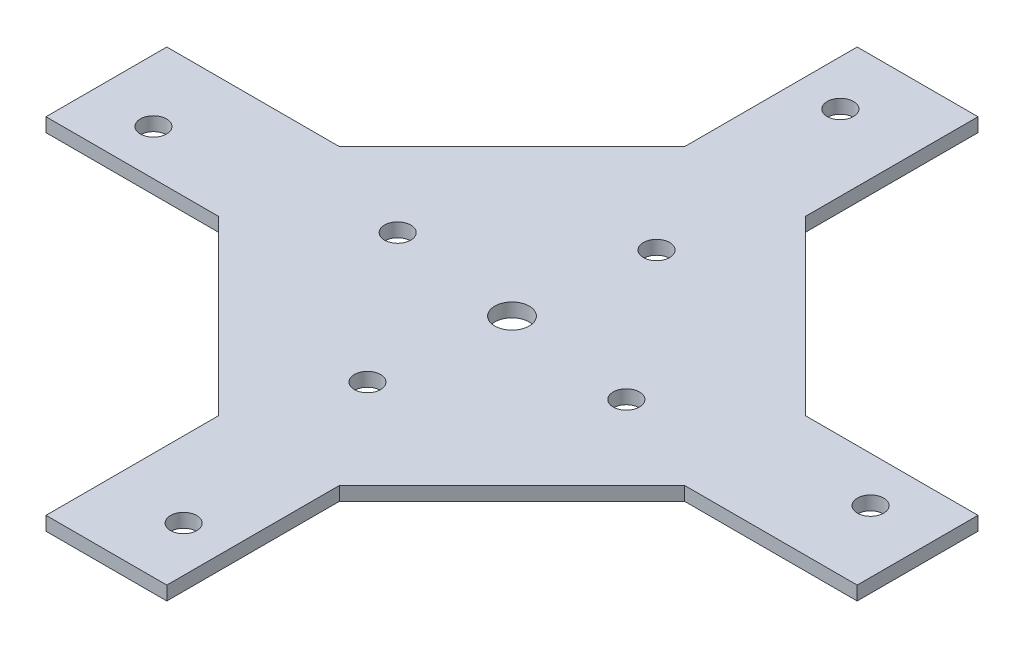
SolidWorks part; units mm, degrees
material "1023 Carbon Steel Sheet (SS)"
ref_plane "Front Plane" through (0, 0, 0) normal (0, 0, 1) x (1, 0, 0)
ref_plane "Top Plane" through (0, 0, 0) normal (0, 1, 0) x (1, 0, 0)
ref_plane "Right Plane" through (0, 0, 0) normal (1, 0, 0) x (0, 0, -1)
sketch "Sketch1" plane through (0, 0, 0) normal (0, 1, 0) x (1, 0, 0)
  line L0 (0, 125.4843) -> (0, -125.4843) construction
  line L2 (173.282, 0) -> (-173.282, 0) construction
  line L3 (-74.6125, -11.1125) -> (-74.6125, 11.1125)
  line L4 (-74.6125, 11.1125) -> (-42.8625, 11.1125)
  line L5 (-74.6125, -11.1125) -> (-42.8625, -11.1125)
  line L6 (-63.1825, -2.7781) -> (-63.1825, 0) construction
  line L7 (-23.8125, 2.7781) -> (-23.8125, 0) construction
  line L8 (-63.1825, -2.7781) -> (0, -2.7781) construction
  line L9 (-23.8125, 2.7781) -> (0, 2.7781) construction
  line L11 (11.1125, 74.6125) -> (11.1125, 42.8625)
  line L12 (-11.1125, 74.6125) -> (11.1125, 74.6125)
  line L13 (-11.1125, 74.6125) -> (-11.1125, 42.8625)
  line L15 (74.6125, -11.1125) -> (42.8625, -11.1125)
  line L16 (74.6125, 11.1125) -> (74.6125, -11.1125)
  line L17 (74.6125, 11.1125) -> (42.8625, 11.1125)
  line L19 (-11.1125, -74.6125) -> (-11.1125, -42.8625)
  line L20 (11.1125, -74.6125) -> (-11.1125, -74.6125)
  line L21 (11.1125, -74.6125) -> (11.1125, -42.8625)
  line L22 (-42.8625, 11.1125) -> (-11.1125, 42.8625) construction
  line L23 (11.1125, 42.8625) -> (42.8625, 11.1125) construction
  line L24 (42.8625, -11.1125) -> (11.1125, -42.8625) construction
  line L25 (-11.1125, -42.8625) -> (-42.8625, -11.1125) construction
  line L26 (-42.8625, 11.1125) -> (-11.1125, 42.8625)
  line L30 (11.1125, 42.8625) -> (42.8625, 11.1125)
  line L31 (42.8625, -11.1125) -> (11.1125, -42.8625)
  line L32 (-42.8625, -11.1125) -> (-11.1125, -42.8625)
  circle A0 centre (-23.8125, 2.7781) radius 2.413
  circle A1 centre (-63.1825, -2.7781) radius 2.413
  circle A8 centre (-2.7781, 63.1825) radius 2.413
  circle A9 centre (2.7781, 23.8125) radius 2.413
  circle A10 centre (63.1825, 2.7781) radius 2.413
  circle A11 centre (23.8125, -2.7781) radius 2.413
  circle A12 centre (2.7781, -63.1825) radius 2.413
  circle A13 centre (-2.7781, -23.8125) radius 2.413
  point P37 (0, 0)
  point P44 (0, 0)
  dimension "D1" = 23.8125
  dimension "D2" = 63.1825
  dimension "D5" = 4.826
  dimension "D3" = 2.7781
  dimension "D4" = 2.7781
extrude "Boss-Extrude1" add sketch "Sketch1" along normal blind 2.54
sketch "Sketch2" plane through (0, 2.54, 0) normal (0, 1, 0) x (1, 0, 0)
  circle A0 centre (0, 0) radius 3.175
  dimension "D1" = 6.35
extrude "Cut-Extrude1" cut sketch "Sketch2" against normal through all
